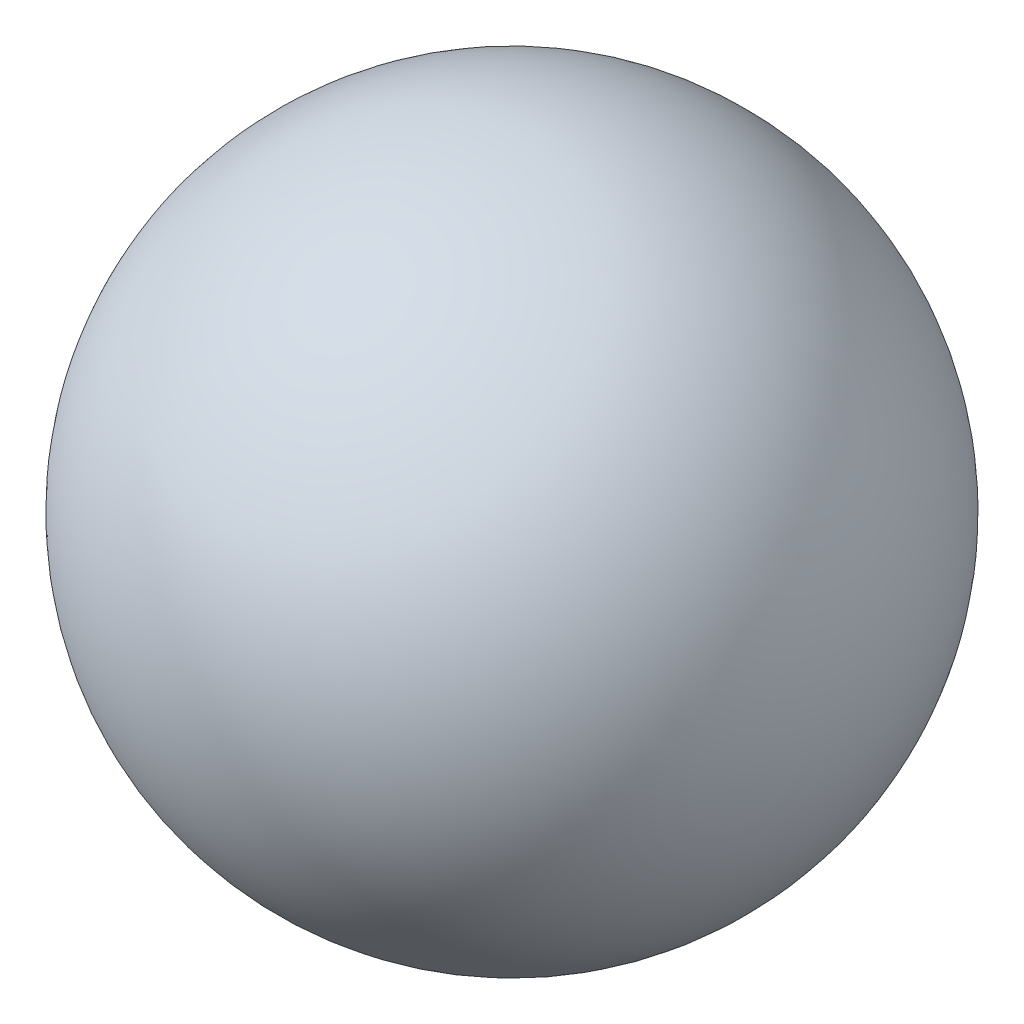
SolidWorks part; units mm, degrees
ref_plane "Front Plane" through (0, 0, 0) normal (0, 0, 1) x (1, 0, 0)
ref_plane "Top Plane" through (0, 0, 0) normal (0, 1, 0) x (1, 0, 0)
ref_plane "Right Plane" through (0, 0, 0) normal (1, 0, 0) x (0, 0, -1)
sketch "Sketch1" plane through (0, 0, 0) normal (0, 0, 1) x (1, 0, 0)
  line L0 (-9, 0) -> (9, 0)
  arc A0 (-9, 0) -> (9, 0) centre (0, 0) cw
  dimension "D1" = 18
revolve "Revolve1" add sketch "Sketch1" angle 360 about L0
